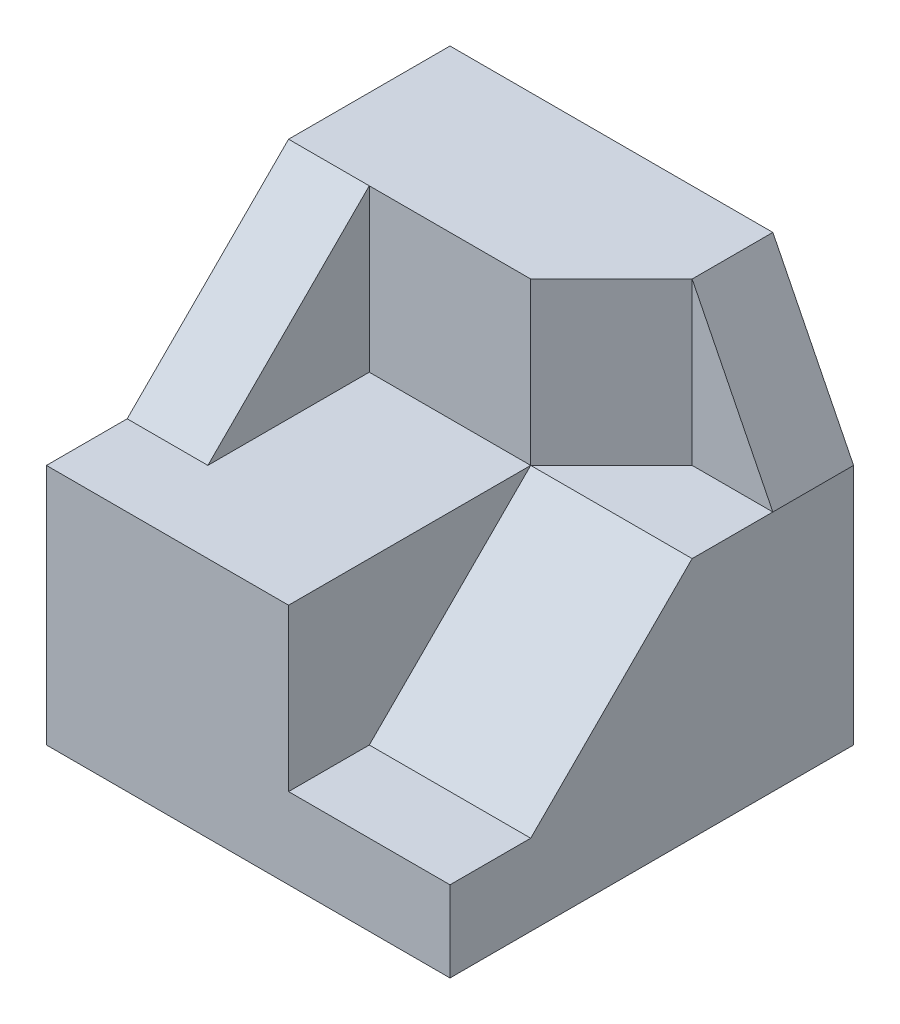
SolidWorks part; units mm, degrees
ref_plane "Front Plane" through (0, 0, 0) normal (0, 0, 1) x (1, 0, 0)
ref_plane "Top Plane" through (0, 0, 0) normal (0, 1, 0) x (1, 0, 0)
ref_plane "Right Plane" through (0, 0, 0) normal (1, 0, 0) x (0, 0, -1)
sketch "Sketch1" plane through (0, 0, 0) normal (0, 0, 1) x (1, 0, 0)
  line L1 (2.5, -2.5) -> (-2.5, -2.5)
  line L2 (2.5, -2.5) -> (2.5, 2.5)
  line L3 (2.5, 2.5) -> (-2.5, 2.5)
  line L4 (-2.5, -2.5) -> (-2.5, 2.5)
  line L5 (2.5, -2.5) -> (-2.5, 2.5) construction
  line L6 (2.5, 2.5) -> (-2.5, -2.5) construction
  point P0 (0, 0)
  dimension "D1" = 5
  dimension "D2" = 5
extrude "Boss-Extrude1" add sketch "Sketch1" along normal blind 5
sketch "Sketch2" plane through (0, 2.5, 0) normal (0, 1, 0) x (1, 0, 0)
  line L0 (-2.5, -5) -> (0.5, -5)
  line L1 (2.5, -5) -> (-2.5, -5) construction
  line L2 (0.5, -5) -> (0.5, -2)
  line L3 (0.5, -2) -> (-1.5, -2)
  line L4 (-1.5, -2) -> (-1.5, -4)
  line L5 (-1.5, -4) -> (-2.5, -4)
  line L6 (-2.5, -5) -> (-2.5, 0) construction
  line L7 (-2.5, -4) -> (-2.5, -5)
  dimension "D1" = 1
  dimension "D2" = 3
  dimension "D3" = 3
  dimension "D4" = 2
extrude "Cut-Extrude1" cut sketch "Sketch2" against normal blind 2
sketch "Sketch3" plane through (-2.5, 0, 0) normal (-1, 0, 0) x (0, 0, 1)
  line L0 (4, 0.5) -> (2, 2.5)
  line L1 (4, 2.5) -> (0, 2.5) construction
  line L2 (2, 2.5) -> (4, 2.5)
  line L3 (4, 2.5) -> (4, 0.5)
  dimension "D1" = 2
extrude "Cut-Extrude7" cut sketch "Sketch3" against normal blind 1
sketch "Sketch6" plane through (0, 0, 5) normal (0, 0, 1) x (1, 0, 0)
  line L0 (0.5, 2.5) -> (2.5, 2.5)
  line L1 (2.5, 2.5) -> (2.5, -1.5)
  line L2 (2.5, -2.5) -> (2.5, 2.5) construction
  line L3 (2.5, -1.5) -> (0.5, -1.5)
  line L4 (0.5, -1.5) -> (0.5, 2.5)
  dimension "D1" = 1
extrude "Cut-Extrude13" cut sketch "Sketch6" against normal blind 1
sketch "Sketch7" plane through (2.5, 0, 0) normal (1, 0, 0) x (0, 0, -1)
  line L0 (-4, 2.5) -> (-2, 2.5)
  line L1 (-4, 2.5) -> (0, 2.5) construction
  line L2 (-2, 2.5) -> (-2, 0.5)
  line L3 (-2, 0.5) -> (-4, -1.5)
  line L4 (-4, -1.5) -> (-4, 2.5)
  line L5 (-5, -2.5) -> (0, -2.5) construction
  dimension "D1" = 2
  dimension "D2" = 3
extrude "Cut-Extrude14" cut sketch "Sketch7" against normal blind 2
sketch "Sketch8" plane through (0, 0, 2) normal (0, 0, 1) x (1, 0, 0)
  line L0 (2.5, 2.5) -> (1.5, 2.5)
  line L1 (2.5, 2.5) -> (-1.5, 2.5) construction
  line L2 (1.5, 2.5) -> (2.5, 0.5)
  line L3 (2.5, 0.5) -> (2.5, 2.5)
  dimension "D1" = 1
extrude "Cut-Extrude16" cut sketch "Sketch8" against normal through all
sketch "Sketch10" plane through (0, 2.5, 0) normal (0, 1, 0) x (1, 0, 0)
  line L0 (2.5, -2) -> (2.5, -1)
  line L1 (2.5, 0) -> (2.5, -2) construction
  line L2 (2.5, -1) -> (1.5, -1)
  line L3 (1.5, 0) -> (1.5, -2) construction
  line L4 (1.5, -1) -> (0.5, -2)
  line L5 (0.5, -2) -> (2.5, -2)
  dimension "D1" = 1
extrude "Cut-Extrude17" cut sketch "Sketch10" against normal blind 2
